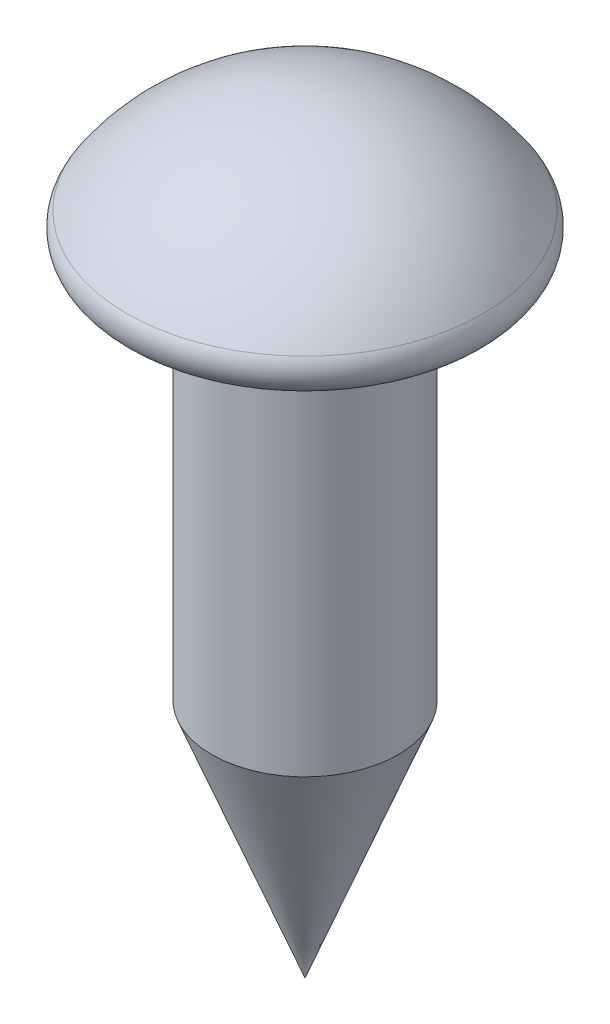
SolidWorks part; units mm, degrees
ref_plane "Front Plane" through (0, 0, 0) normal (0, 0, 1) x (1, 0, 0)
ref_plane "Top Plane" through (0, 0, 0) normal (0, 1, 0) x (1, 0, 0)
ref_plane "Right Plane" through (0, 0, 0) normal (1, 0, 0) x (0, 0, -1)
sketch "Sketch1" plane through (0, 0, 0) normal (0, 0, 1) x (1, 0, 0)
  line L0 (-2.4003, 0) -> (2.4003, 0)
  line L1 (-1.4224, -5.8673) -> (0, -9.525)
  line L2 (-1.4224, -5.8673) -> (1.4224, -5.8673)
  line L3 (-1.4224, -5.8673) -> (-1.4224, 0)
  line L4 (-1.4224, 0) -> (1.4224, 0)
  line L5 (1.4224, -5.8673) -> (1.4224, 0)
  line L6 (-1.4224, -5.8673) -> (1.4224, 0) construction
  line L7 (-1.4224, 0) -> (1.4224, -5.8673) construction
  line L8 (0, -9.525) -> (1.4224, -5.8673)
  line L9 (0, -9.525) -> (0, 2.032) construction
  line L10 (0, 2.032) -> (0, -9.525)
  arc A1 (2.4003, 0) -> (2.7153, 0.5953) centre (2.4003, 0.381) ccw
  arc A2 (-2.4003, 0) -> (-2.7153, 0.5953) centre (-2.4003, 0.381) cw
  arc A3 (2.7153, 0.5953) -> (-2.7153, 0.5953) centre (0, -1.2523) ccw
  point P6 (2.8301, 0)
  point P9 (-2.8301, 0)
  point P10 (-2.7813, 0.381)
  point P11 (2.7813, 0.381)
  point P12 (0, -2.9337)
  point P17 (0, 2.8301)
  point P18 (0, 2.032)
  dimension "D1" = 2.8448
  dimension "D5" = 0.381
  dimension "D2" = 5.5626
  dimension "D3" = 9.525
  dimension "D4" = 2.032
  dimension "D6" = 42.5
revolve "Revolve5" add sketch "Sketch1" angle 360 about L10
